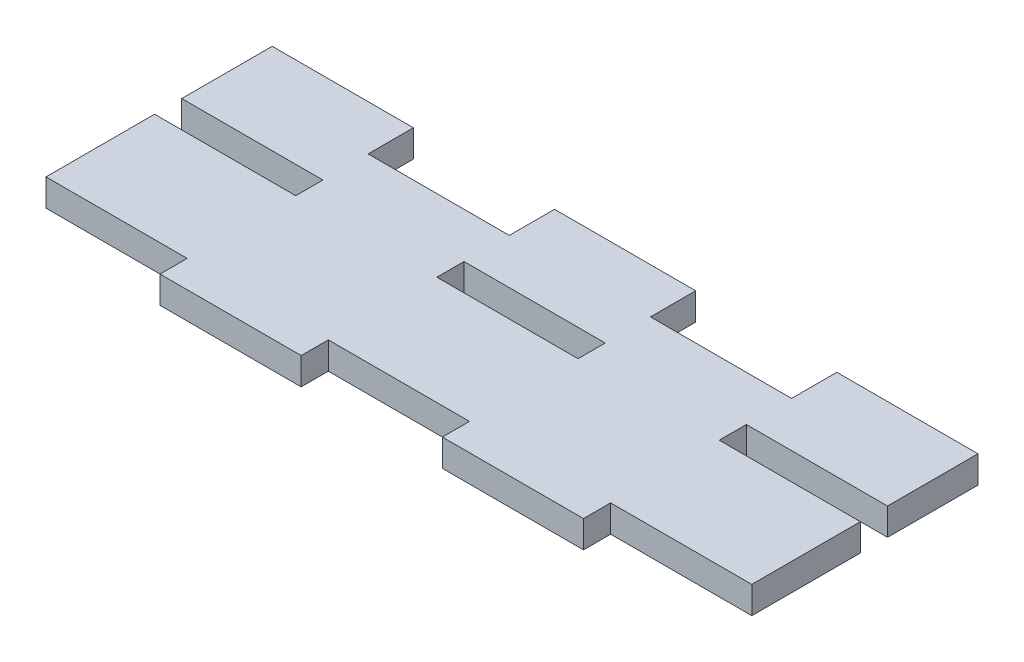
SolidWorks part; units mm, degrees
ref_plane "Front Plane" through (0, 0, 0) normal (0, 0, 1) x (1, 0, 0)
ref_plane "Top Plane" through (0, 0, 0) normal (0, 1, 0) x (1, 0, 0)
ref_plane "Right Plane" through (0, 0, 0) normal (1, 0, 0) x (0, 0, -1)
sketch "Sketch1" plane through (0, 0, 0) normal (0, 1, 0) x (1, 0, 0)
  line L0 (-23.4, 5) -> (-7.8, 5)
  line L1 (-39, 10) -> (-23.4, 10)
  line L2 (-39, 10) -> (-39, 0)
  line L4 (39, 10) -> (39, 0)
  line L6 (-7.8, 10) -> (7.8, 10)
  line L8 (23.4, 10) -> (39, 10)
  line L9 (-23.4, 10) -> (-23.4, 5)
  line L10 (-7.8, 10) -> (-7.8, 5)
  line L11 (7.8, 10) -> (7.8, 5)
  line L12 (23.4, 10) -> (23.4, 5)
  line L13 (7.8, 5) -> (23.4, 5)
  line L14 (-39, 0) -> (-23.4, 0)
  line L15 (-39, -3) -> (-23.4, -3)
  line L16 (-39, -15) -> (-23.4, -15)
  line L17 (-7.8, 0) -> (7.8, 0)
  line L18 (-7.8, -3) -> (7.8, -3)
  line L19 (23.4, 0) -> (39, 0)
  line L20 (-23.4, 0) -> (-23.4, -3)
  line L21 (-7.8, 0) -> (-7.8, -3)
  line L22 (7.8, 0) -> (7.8, -3)
  line L23 (23.4, 0) -> (23.4, -3)
  line L24 (-39, -3) -> (-39, -15)
  line L25 (39, -3) -> (39, -15)
  line L26 (23.4, -3) -> (39, -3)
  line L27 (-23.4, -18) -> (-7.8, -18)
  line L29 (7.8, -18) -> (23.4, -18)
  line L31 (-23.4, -18) -> (-23.4, -15)
  line L32 (-7.8, -18) -> (-7.8, -15)
  line L33 (7.8, -18) -> (7.8, -15)
  line L34 (23.4, -18) -> (23.4, -15)
  line L35 (-7.8, -15) -> (7.8, -15)
  line L36 (23.4, -15) -> (39, -15)
  point P0 (0, 0)
  dimension "D1" = 78
  dimension "D3" = 5
  dimension "D4" = 5
  dimension "D5" = 3
  dimension "D6" = 12
extrude "Boss-Extrude1" add sketch "Sketch1" along normal blind 3
